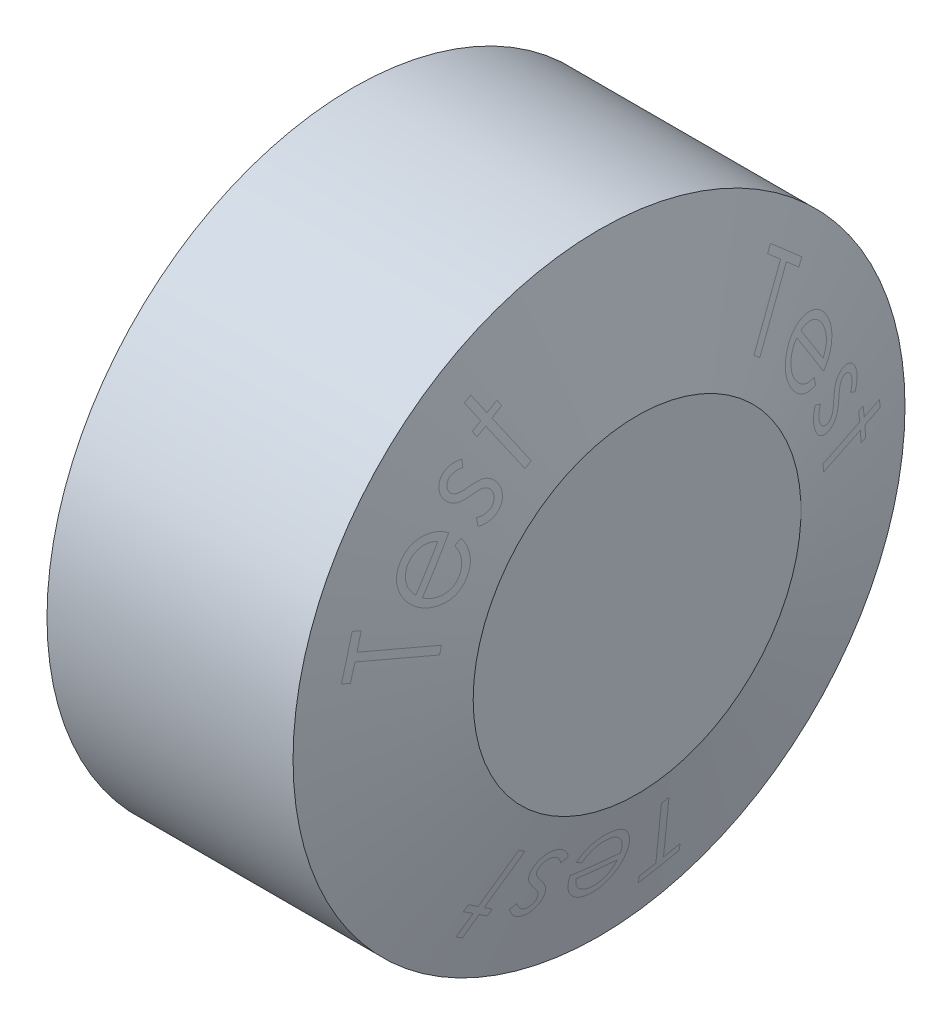
SolidWorks part; units mm, degrees
ref_plane "Ebene vorne" through (0, 0, 0) normal (0, 0, 1) x (1, 0, 0)
ref_plane "Ebene oben" through (0, 0, 0) normal (0, 1, 0) x (1, 0, 0)
ref_plane "Ebene rechts" through (0, 0, 0) normal (1, 0, 0) x (0, 0, -1)
sketch "Skizze1" plane through (0, 0, 0) normal (0, 0, 1) x (1, 0, 0)
  line L0 (0, 0) -> (56.0834, 0) construction
  line L1 (0, 0) -> (0, -14)
  line L2 (0, -14) -> (11.2583, -14)
  line L3 (11.2583, -14) -> (13, -7.5)
  line L4 (13, -7.5) -> (13, 0)
  line L5 (0, 0) -> (13, 0)
  dimension "D1" = 28
  dimension "D2" = 15
  dimension "D3" = 13
  dimension "D4" = 15
revolve "Rotation1" add sketch "Skizze1" angle 360 about L0
sketch "Skizze13" plane through (13, 0, 0) normal (1, 0, 0) x (0, 0, -1)
  circle A1 centre (0, 0) radius 8.9821 construction
  text T0 "Test       Test       Test"
split line "Trennlinie1"
